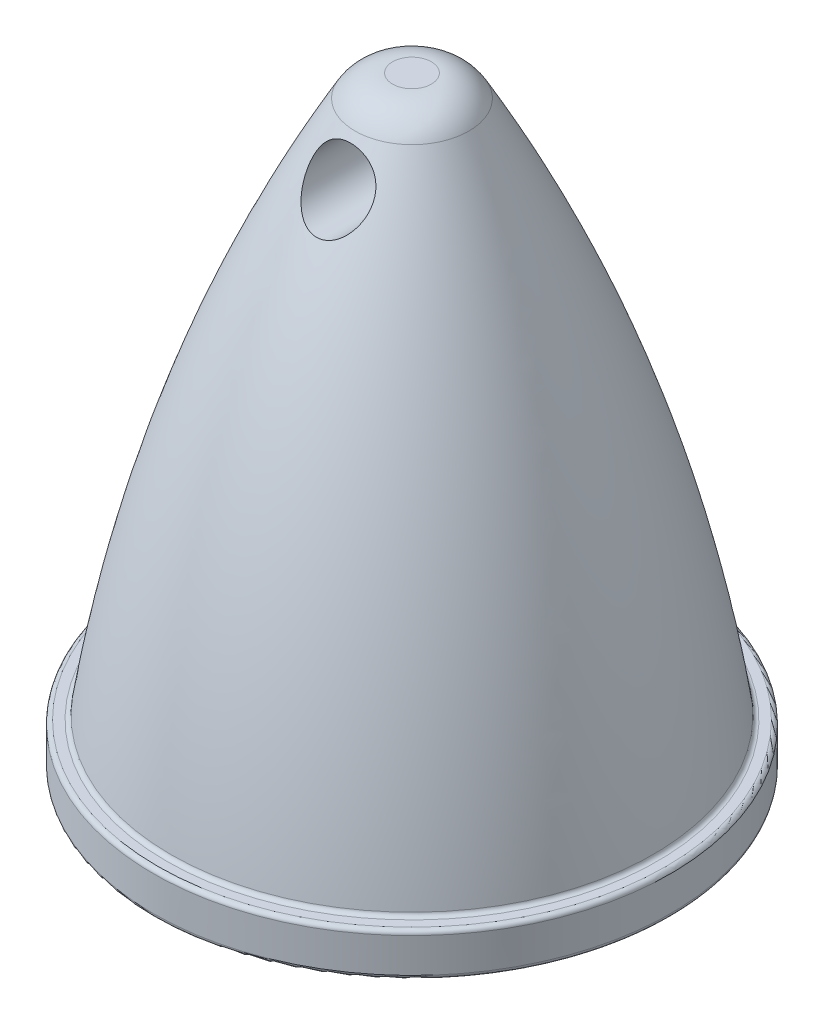
SolidWorks part; units mm, degrees
material "1060 Alloy"
ref_plane "Front Plane" through (0, 0, 0) normal (0, 0, 1) x (1, 0, 0)
ref_plane "Top Plane" through (0, 0, 0) normal (0, 1, 0) x (1, 0, 0)
ref_plane "Right Plane" through (0, 0, 0) normal (1, 0, 0) x (0, 0, -1)
sketch "Sketch1" plane through (0, 0, 0) normal (0, 0, 1) x (1, 0, 0)
  line L0 (0, 0) -> (0, 15)
  line L1 (0, 0) -> (-6, 0)
  line L2 (-6, 0) -> (-6, 1)
  line L3 (-6, 1) -> (-5.6088, 1)
  line L4 (-0.4223, 15) -> (0, 15)
  spline S0 degree 2 poles (-5.6088, 1) (-4.4747, 8.5437) (-0.4223, 15) knots 0 0 0 1 1 1
revolve "Revolve1" add sketch "Sketch1" angle 360 about L0
sketch "Sketch2" plane through (0, 15, 0) normal (0, 1, 0) x (1, 0, 0)
  circle A0 centre (0, 0) radius 1.1037
extrude "Cut-Extrude1" cut sketch "Sketch2" against normal blind 1
fillet "Fillet1" radius 1 1 edges at (0, 14, -1.0286)
sketch "Sketch3" plane through (0, 0, 0) normal (0, 0, 1) x (1, 0, 0)
  circle A0 centre (0, 12.5541) radius 0.75
extrude "Cut-Extrude2" cut sketch "Sketch3" against normal blind 3 and the other way blind 10
fillet "Fillet2" radius 0.1 3 edges at (0, 0, -6) (0, 1, -5.6088) (0, 1, -6)
sketch "Sketch4" plane through (0, 0, 0) normal (0, -1, 0) x (1, 0, 0)
  circle A0 centre (0, 0) radius 3
extrude "Cut-Extrude3" cut sketch "Sketch4" against normal blind 10
